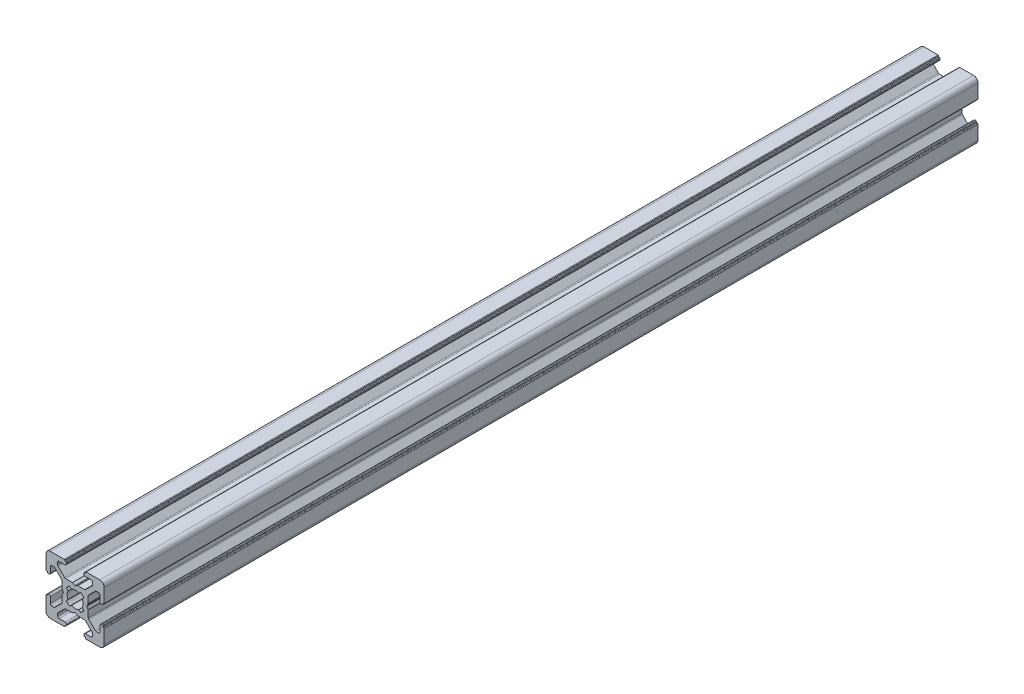
SolidWorks part; units mm, degrees
material "6061 Alloy"
ref_plane "Front Plane" through (0, 0, 0) normal (0, 0, 1) x (1, 0, 0)
ref_plane "Top Plane" through (0, 0, 0) normal (0, 1, 0) x (1, 0, 0)
ref_plane "Right Plane" through (0, 0, 0) normal (1, 0, 0) x (0, 0, -1)
sketch "Sketch1" plane through (0, 0, 0) normal (0, 0, 1) x (1, 0, 0)
  line L0 (0, 13.3675) -> (0, -10.9159) construction
  line L1 (-12.9725, 0) -> (15.1887, 0) construction
  line L2 (-3.5, 8.5) -> (-5.5, 8.5)
  line L3 (-3.55, 9.7) -> (-3.55, 9.8)
  line L4 (-6, 7.2678) -> (-6, 8)
  line L5 (-7.2678, 6) -> (-8, 6)
  line L6 (-3.75, 10) -> (-8.5, 10)
  line L7 (-9.7, 3.55) -> (-9.8, 3.55)
  line L8 (-9.5, 3.2) -> (-9.5, 3.35)
  line L9 (-9, 3) -> (-9.3, 3)
  line L10 (-4.4732, 0.8536) -> (-4.0381, 0.1)
  line L11 (-4.5, 3.2322) -> (-4.5, 0.9536)
  line L12 (-8.5, 3.5) -> (-8.5, 5.5)
  line L13 (-10, 3.75) -> (-10, 8.5)
  line L14 (-3.5858, 4.6464) -> (-5.8536, 6.9142)
  line L15 (-4.6464, 3.5858) -> (-6.9142, 5.8536)
  line L16 (-3.2, 9.5) -> (-3.35, 9.5)
  line L17 (-3, 9) -> (-3, 9.3)
  line L18 (-0.8536, 4.4732) -> (-0.1, 4.0381)
  line L19 (-3.2322, 4.5) -> (-0.9536, 4.5)
  line L20 (-1.2582, 2.4453) -> (-1.9139, 2.9896)
  line L21 (-2.4453, 1.2582) -> (-2.9922, 1.9099)
  line L22 (3.5, -8.5) -> (5.5, -8.5)
  line L23 (3.55, -9.7) -> (3.55, -9.8)
  line L24 (6, -7.2678) -> (6, -8)
  line L25 (7.2678, -6) -> (8, -6)
  line L26 (3.75, -10) -> (8.5, -10)
  line L27 (9.7, -3.55) -> (9.8, -3.55)
  line L28 (9.5, -3.2) -> (9.5, -3.35)
  line L29 (9, -3) -> (9.3, -3)
  line L30 (4.4732, -0.8536) -> (4.0381, -0.1)
  line L31 (4.5, -3.2322) -> (4.5, -0.9536)
  line L32 (8.5, -3.5) -> (8.5, -5.5)
  line L33 (10, -3.75) -> (10, -8.5)
  line L34 (3.5858, -4.6464) -> (5.8536, -6.9142)
  line L35 (4.6464, -3.5858) -> (6.9142, -5.8536)
  line L36 (3.2, -9.5) -> (3.35, -9.5)
  line L37 (3, -9) -> (3, -9.3)
  line L38 (0.8536, -4.4732) -> (0.1, -4.0381)
  line L39 (3.2322, -4.5) -> (0.9536, -4.5)
  line L40 (1.2582, -2.4453) -> (1.9139, -2.9896)
  line L41 (2.4453, -1.2582) -> (2.9922, -1.9099)
  line L42 (-2.4453, -1.2582) -> (-2.9922, -1.9099)
  line L43 (-1.2582, -2.4453) -> (-1.9139, -2.9896)
  line L44 (-3.2322, -4.5) -> (-0.9536, -4.5)
  line L45 (-0.8536, -4.4732) -> (-0.1, -4.0381)
  line L46 (-3, -9) -> (-3, -9.3)
  line L47 (-3.2, -9.5) -> (-3.35, -9.5)
  line L48 (-4.6464, -3.5858) -> (-6.9142, -5.8536)
  line L49 (-3.5858, -4.6464) -> (-5.8536, -6.9142)
  line L50 (-10, -3.75) -> (-10, -8.5)
  line L51 (-8.5, -3.5) -> (-8.5, -5.5)
  line L52 (-4.5, -3.2322) -> (-4.5, -0.9536)
  line L53 (-4.4732, -0.8536) -> (-4.0381, -0.1)
  line L54 (-9, -3) -> (-9.3, -3)
  line L55 (-9.5, -3.2) -> (-9.5, -3.35)
  line L56 (-9.7, -3.55) -> (-9.8, -3.55)
  line L57 (2.4453, 1.2582) -> (2.9922, 1.9099)
  line L58 (1.2582, 2.4453) -> (1.9139, 2.9896)
  line L59 (3.2322, 4.5) -> (0.9536, 4.5)
  line L60 (0.8536, 4.4732) -> (0.1, 4.0381)
  line L61 (-3.75, -10) -> (-8.5, -10)
  line L62 (-7.2678, -6) -> (-8, -6)
  line L63 (-6, -7.2678) -> (-6, -8)
  line L64 (3, 9) -> (3, 9.3)
  line L65 (3.2, 9.5) -> (3.35, 9.5)
  line L66 (4.6464, 3.5858) -> (6.9142, 5.8536)
  line L67 (3.5858, 4.6464) -> (5.8536, 6.9142)
  line L68 (10, 3.75) -> (10, 8.5)
  line L69 (8.5, 3.5) -> (8.5, 5.5)
  line L70 (4.5, 3.2322) -> (4.5, 0.9536)
  line L71 (4.4732, 0.8536) -> (4.0381, 0.1)
  line L72 (9, 3) -> (9.3, 3)
  line L73 (9.5, 3.2) -> (9.5, 3.35)
  line L74 (9.7, 3.55) -> (9.8, 3.55)
  line L75 (3.75, 10) -> (8.5, 10)
  line L76 (7.2678, 6) -> (8, 6)
  line L77 (6, 7.2678) -> (6, 8)
  line L78 (3.55, 9.7) -> (3.55, 9.8)
  line L79 (3.5, 8.5) -> (5.5, 8.5)
  line L80 (-3.55, -9.7) -> (-3.55, -9.8)
  line L81 (-3.5, -8.5) -> (-5.5, -8.5)
  arc A0 (-10, 8.5) -> (-8.5, 10) centre (-8.5, 8.5) cw
  arc A1 (-8.5, 5.5) -> (-8, 6) centre (-8, 5.5) cw
  arc A2 (-7.2678, 6) -> (-6.9142, 5.8536) centre (-7.2678, 5.5) cw
  arc A3 (-5.8536, 6.9142) -> (-6, 7.2678) centre (-5.5, 7.2678) cw
  arc A4 (-6, 8) -> (-5.5, 8.5) centre (-5.5, 8) cw
  arc A5 (-9.7, 3.55) -> (-9.5, 3.35) centre (-9.7, 3.35) cw
  arc A6 (-9.8, 3.55) -> (-10, 3.75) centre (-9.8, 3.75) cw
  arc A7 (-9.3, 3) -> (-9.5, 3.2) centre (-9.3, 3.2) cw
  arc A8 (-8.5, 3.5) -> (-9, 3) centre (-9, 3.5) cw
  arc A9 (-4.6464, 3.5858) -> (-4.5, 3.2322) centre (-5, 3.2322) cw
  arc A10 (-4.4732, 0.8536) -> (-4.5, 0.9536) centre (-4.3, 0.9536) cw
  arc A11 (-4.0381, 0.1) -> (-4.0381, -0.1) centre (-4.2113, 0) cw
  arc A12 (-3.2, 9.5) -> (-3, 9.3) centre (-3.2, 9.3) cw
  arc A13 (-0.9536, 4.5) -> (-0.8536, 4.4732) centre (-0.9536, 4.3) cw
  arc A14 (-2.9922, 1.9099) -> (-1.9139, 2.9896) centre (0, 0) cw
  arc A15 (-3.2322, 4.5) -> (-3.5858, 4.6464) centre (-3.2322, 5) cw
  arc A16 (-3.75, 10) -> (-3.55, 9.8) centre (-3.75, 9.8) cw
  arc A17 (-3.35, 9.5) -> (-3.55, 9.7) centre (-3.35, 9.7) cw
  arc A18 (2.4453, -1.2582) -> (2.4453, 1.2582) centre (0, 0) ccw
  arc A19 (-3, 9) -> (-3.5, 8.5) centre (-3.5, 9) cw
  arc A20 (-2.4453, -1.2582) -> (-2.4453, 1.2582) centre (0, 0) cw
  arc A21 (10, -8.5) -> (8.5, -10) centre (8.5, -8.5) cw
  arc A22 (8.5, -5.5) -> (8, -6) centre (8, -5.5) cw
  arc A23 (7.2678, -6) -> (6.9142, -5.8536) centre (7.2678, -5.5) cw
  arc A24 (5.8536, -6.9142) -> (6, -7.2678) centre (5.5, -7.2678) cw
  arc A25 (6, -8) -> (5.5, -8.5) centre (5.5, -8) cw
  arc A26 (9.7, -3.55) -> (9.5, -3.35) centre (9.7, -3.35) cw
  arc A27 (9.8, -3.55) -> (10, -3.75) centre (9.8, -3.75) cw
  arc A28 (9.3, -3) -> (9.5, -3.2) centre (9.3, -3.2) cw
  arc A29 (8.5, -3.5) -> (9, -3) centre (9, -3.5) cw
  arc A30 (4.6464, -3.5858) -> (4.5, -3.2322) centre (5, -3.2322) cw
  arc A31 (4.4732, -0.8536) -> (4.5, -0.9536) centre (4.3, -0.9536) cw
  arc A32 (3.2, -9.5) -> (3, -9.3) centre (3.2, -9.3) cw
  arc A33 (-0.1, -4.0381) -> (0.1, -4.0381) centre (0, -4.2113) cw
  arc A34 (0.9536, -4.5) -> (0.8536, -4.4732) centre (0.9536, -4.3) cw
  arc A35 (2.9922, -1.9099) -> (1.9139, -2.9896) centre (0, 0) cw
  arc A36 (1.2582, -2.4453) -> (-1.2582, -2.4453) centre (0, 0) cw
  arc A37 (3.2322, -4.5) -> (3.5858, -4.6464) centre (3.2322, -5) cw
  arc A38 (3.75, -10) -> (3.55, -9.8) centre (3.75, -9.8) cw
  arc A39 (3.35, -9.5) -> (3.55, -9.7) centre (3.35, -9.7) cw
  arc A40 (3, -9) -> (3.5, -8.5) centre (3.5, -9) cw
  arc A41 (-3, -9) -> (-3.5, -8.5) centre (-3.5, -9) ccw
  arc A42 (-3.35, -9.5) -> (-3.55, -9.7) centre (-3.35, -9.7) ccw
  arc A43 (-3.75, -10) -> (-3.55, -9.8) centre (-3.75, -9.8) ccw
  arc A44 (-3.2322, -4.5) -> (-3.5858, -4.6464) centre (-3.2322, -5) ccw
  arc A45 (-2.9922, -1.9099) -> (-1.9139, -2.9896) centre (0, 0) ccw
  arc A46 (-0.9536, -4.5) -> (-0.8536, -4.4732) centre (-0.9536, -4.3) ccw
  arc A47 (-3.2, -9.5) -> (-3, -9.3) centre (-3.2, -9.3) ccw
  arc A48 (-4.4732, -0.8536) -> (-4.5, -0.9536) centre (-4.3, -0.9536) ccw
  arc A49 (3, 9) -> (3.5, 8.5) centre (3.5, 9) ccw
  arc A50 (3.35, 9.5) -> (3.55, 9.7) centre (3.35, 9.7) ccw
  arc A51 (3.75, 10) -> (3.55, 9.8) centre (3.75, 9.8) ccw
  arc A52 (3.2322, 4.5) -> (3.5858, 4.6464) centre (3.2322, 5) ccw
  arc A53 (1.2582, 2.4453) -> (-1.2582, 2.4453) centre (0, 0) ccw
  arc A54 (-4.6464, -3.5858) -> (-4.5, -3.2322) centre (-5, -3.2322) ccw
  arc A55 (-8.5, -3.5) -> (-9, -3) centre (-9, -3.5) ccw
  arc A56 (-9.3, -3) -> (-9.5, -3.2) centre (-9.3, -3.2) ccw
  arc A57 (-9.8, -3.55) -> (-10, -3.75) centre (-9.8, -3.75) ccw
  arc A58 (-9.7, -3.55) -> (-9.5, -3.35) centre (-9.7, -3.35) ccw
  arc A59 (-6, -8) -> (-5.5, -8.5) centre (-5.5, -8) ccw
  arc A60 (2.9922, 1.9099) -> (1.9139, 2.9896) centre (0, 0) ccw
  arc A61 (0.9536, 4.5) -> (0.8536, 4.4732) centre (0.9536, 4.3) ccw
  arc A62 (-0.1, 4.0381) -> (0.1, 4.0381) centre (0, 4.2113) ccw
  arc A63 (-5.8536, -6.9142) -> (-6, -7.2678) centre (-5.5, -7.2678) ccw
  arc A64 (-7.2678, -6) -> (-6.9142, -5.8536) centre (-7.2678, -5.5) ccw
  arc A65 (-8.5, -5.5) -> (-8, -6) centre (-8, -5.5) ccw
  arc A66 (-10, -8.5) -> (-8.5, -10) centre (-8.5, -8.5) ccw
  arc A67 (3.2, 9.5) -> (3, 9.3) centre (3.2, 9.3) ccw
  arc A68 (4.0381, 0.1) -> (4.0381, -0.1) centre (4.2113, 0) ccw
  arc A69 (4.4732, 0.8536) -> (4.5, 0.9536) centre (4.3, 0.9536) ccw
  arc A70 (4.6464, 3.5858) -> (4.5, 3.2322) centre (5, 3.2322) ccw
  arc A71 (8.5, 3.5) -> (9, 3) centre (9, 3.5) ccw
  arc A72 (9.3, 3) -> (9.5, 3.2) centre (9.3, 3.2) ccw
  arc A73 (9.8, 3.55) -> (10, 3.75) centre (9.8, 3.75) ccw
  arc A74 (9.7, 3.55) -> (9.5, 3.35) centre (9.7, 3.35) ccw
  arc A75 (6, 8) -> (5.5, 8.5) centre (5.5, 8) ccw
  arc A76 (5.8536, 6.9142) -> (6, 7.2678) centre (5.5, 7.2678) ccw
  arc A77 (7.2678, 6) -> (6.9142, 5.8536) centre (7.2678, 5.5) ccw
  arc A78 (8.5, 5.5) -> (8, 6) centre (8, 5.5) ccw
  arc A79 (10, 8.5) -> (8.5, 10) centre (8.5, 8.5) ccw
  dimension "D4" = 5.5
  dimension "D1" = 6
  dimension "D2" = 20
  dimension "D3" = 20
  dimension "D5" = 5.5
  dimension "D6" = 10
  dimension "D7" = 6
  dimension "D8" = 6
  dimension "D9" = 6
extrude "Extrude1" add sketch "Sketch1" along normal blind 300
